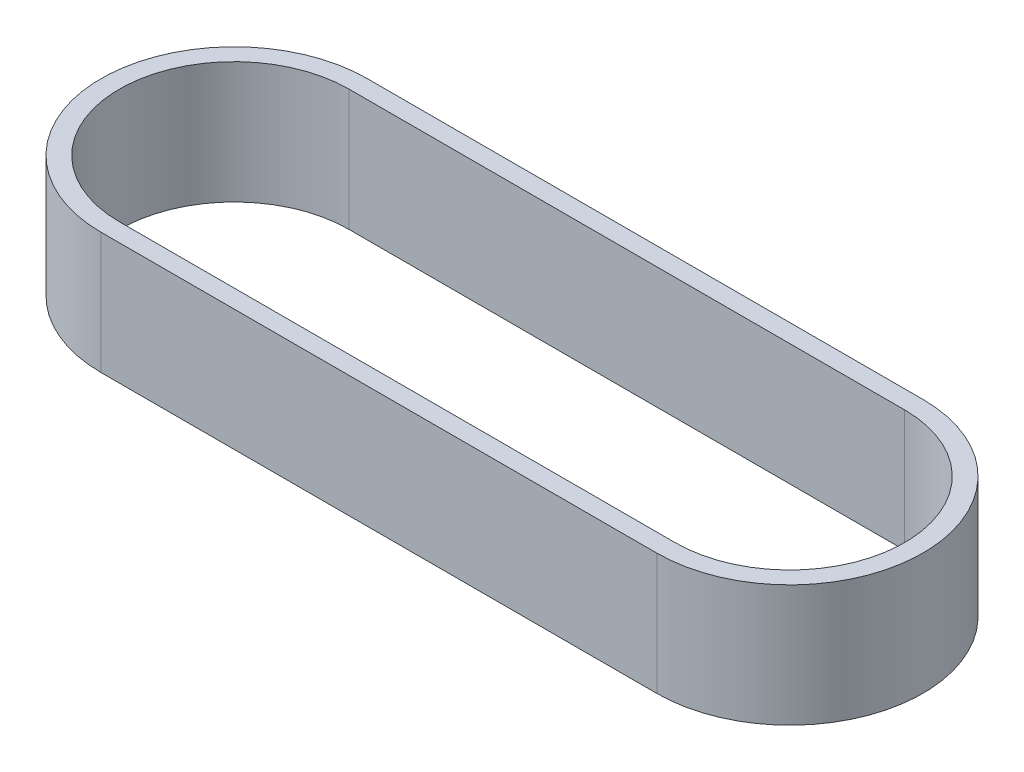
SolidWorks part; units mm, degrees
ref_plane "Front Plane" through (0, 0, 0) normal (0, 0, 1) x (1, 0, 0)
ref_plane "Top Plane" through (0, 0, 0) normal (0, 1, 0) x (1, 0, 0)
ref_plane "Right Plane" through (0, 0, 0) normal (1, 0, 0) x (0, 0, -1)
sketch "Sketch2" plane through (0, 0, 0) normal (0, 1, 0) x (1, 0, 0)
  line L0 (0, 0) -> (0, 18.7397) construction
  line L1 (0, 0) -> (0, -19.9308) construction
  line L2 (0, 0) -> (45.72, 0) construction
  line L3 (45.72, 0) -> (45.72, 18.7397) construction
  line L4 (45.72, 0) -> (45.72, -19.3876) construction
  line L5 (0, 10.95) -> (45.72, 10.95)
  line L6 (0, 9.45) -> (45.72, 9.45)
  line L7 (0, -9.45) -> (45.72, -9.45)
  line L8 (0, -10.95) -> (45.72, -10.95)
  arc A0 (0, 9.45) -> (0, -9.45) centre (0, 0) ccw
  arc A1 (0, 10.95) -> (0, -10.95) centre (0, 0) ccw
  arc A2 (45.72, -9.45) -> (45.72, 9.45) centre (45.72, 0) ccw
  arc A3 (45.72, -10.95) -> (45.72, 10.95) centre (45.72, 0) ccw
  dimension "D1" = 18.9
  dimension "D2" = 1.5
  dimension "D3" = 18.9
  dimension "D4" = 1.5
  dimension "D5" = 45.72
extrude "Boss-Extrude1" add sketch "Sketch2" along normal blind 10
sketch "Sketch3" plane through (0, 10, 0) normal (0, 1, 0) x (1, 0, 0)
  line L0 (45.72, 0) -> (60.782, 0) construction
  line L1 (0, 0) -> (-15.4482, 0) construction
